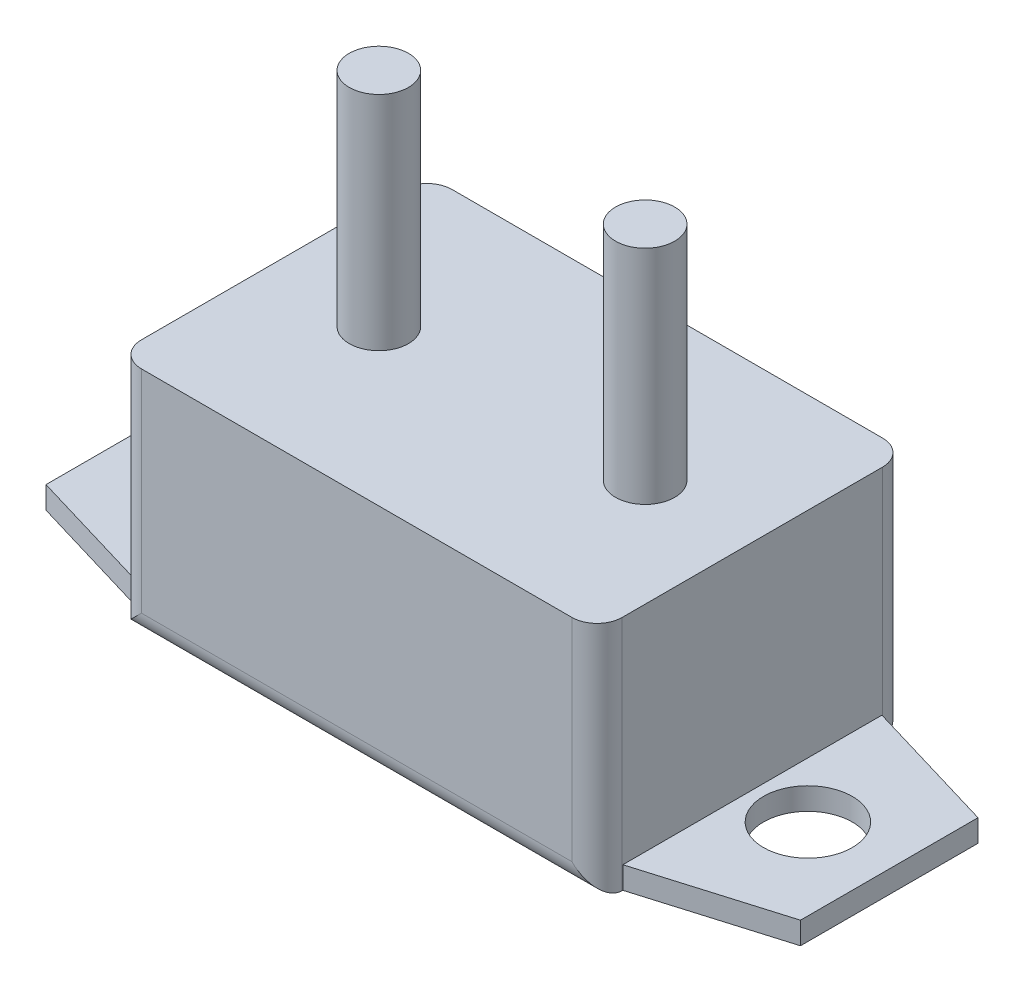
SolidWorks part; units mm, degrees
ref_plane "Alzado" through (0, 0, 0) normal (0, 0, 1) x (1, 0, 0)
ref_plane "Planta" through (0, 0, 0) normal (0, 1, 0) x (1, 0, 0)
ref_plane "Vista lateral" through (0, 0, 0) normal (1, 0, 0) x (0, 0, -1)
sketch "Croquis1" plane through (0, 0, 0) normal (0, 1, 0) x (1, 0, 0)
  line L1 (-16.25, 10.5) -> (16.25, 10.5)
  line L2 (-16.25, 10.5) -> (-16.25, -10.5)
  line L3 (-16.25, -10.5) -> (16.25, -10.5)
  line L4 (16.25, 10.5) -> (16.25, -10.5)
  line L5 (-16.25, 10.5) -> (16.25, -10.5) construction
  line L6 (-16.25, -10.5) -> (16.25, 10.5) construction
  point P0 (0, 0)
  dimension "D1" = 32.5
  dimension "D2" = 21
extrude "Saliente-Extruir1" add sketch "Croquis1" along normal blind 16
sketch "Croquis2" plane through (0, 16, 0) normal (0, 1, 0) x (1, 0, 0)
  line L0 (0, 7.2145) -> (0, -6.1456) construction
  circle A0 centre (-9, 0) radius 2
  circle A1 centre (9, 0) radius 2
  dimension "D1" = 4
  dimension "D2" = 18
extrude "Saliente-Extruir2" add sketch "Croquis2" along normal blind 15
sketch "Croquis3" plane through (0, 0, 0) normal (0, -1, 0) x (1, 0, 0)
  line L0 (0, 14.8491) -> (0, -15.0707) construction
  line L1 (-16.25, 8.7543) -> (-25.5, 6)
  line L2 (-16.25, -10.5) -> (-16.25, 10.5) construction
  line L3 (-25.5, 6) -> (-25.5, -6)
  line L4 (-16.25, 8.7543) -> (-16.25, -8.7543)
  line L5 (-33.2442, 0) -> (-9.7388, 0) construction
  line L6 (-16.25, -8.7543) -> (-25.5, -6)
  line L7 (16.25, -8.7543) -> (25.5, -6)
  line L8 (16.25, 8.7543) -> (16.25, -8.7543)
  line L9 (25.5, 6) -> (25.5, -6)
  line L10 (16.25, 8.7543) -> (25.5, 6)
  line L11 (-17, 5.1049) -> (-17, -9.1209) construction
  line L12 (17, 5.1049) -> (17, -4.7177) construction
  circle A0 centre (-20, 0) radius 3
  circle A1 centre (20, 0) radius 3
  point P8 (25.5, 0)
  point P12 (-16.25, 0)
  point P13 (-25.5, 0)
  point P14 (16.25, 0)
  dimension "D2" = 6
  dimension "D1" = 51
  dimension "D3" = 12
  dimension "D4" = 34
extrude "Saliente-Extruir3" add sketch "Croquis3" against normal blind 1.5
fillet "Redondeo1" radius 1.7 6 edges at (-16.25, 8, -10.5) (16.25, 8, -10.5) (-16.25, 8, 10.5) (0, 0, -10.5) (16.25, 8, 10.5) (0, 0, 10.5)
